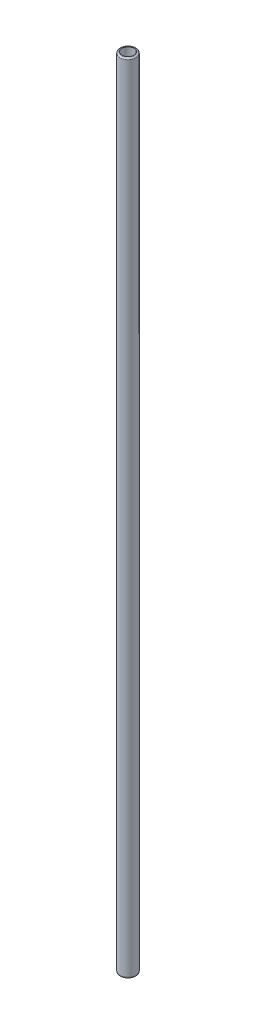
SolidWorks part; units mm, degrees
material "ABS"
ref_plane "Front Plane" through (0, 0, 0) normal (0, 0, 1) x (1, 0, 0)
ref_plane "Top Plane" through (0, 0, 0) normal (0, 1, 0) x (1, 0, 0)
ref_plane "Right Plane" through (0, 0, 0) normal (1, 0, 0) x (0, 0, -1)
sketch "Sketch1" plane through (0, 0, 0) normal (0, 1, 0) x (1, 0, 0)
  circle A0 centre (0, 0) radius 6
  circle A1 centre (0, 0) radius 4.5
extrude "Boss-Extrude1" add sketch "Sketch1" along normal blind 600
cosmetic thread "Cosmetic Thread2" parameters "D1"=35, "D2"=6.647
cosmetic thread "Cosmetic Thread3" parameters "D1"=35, "D2"=6.647
fillet "Fillet3" radius 1 1 edges at (0, 0, 6)
fillet "Fillet4" radius 1 1 edges at (0, 600, 6)
